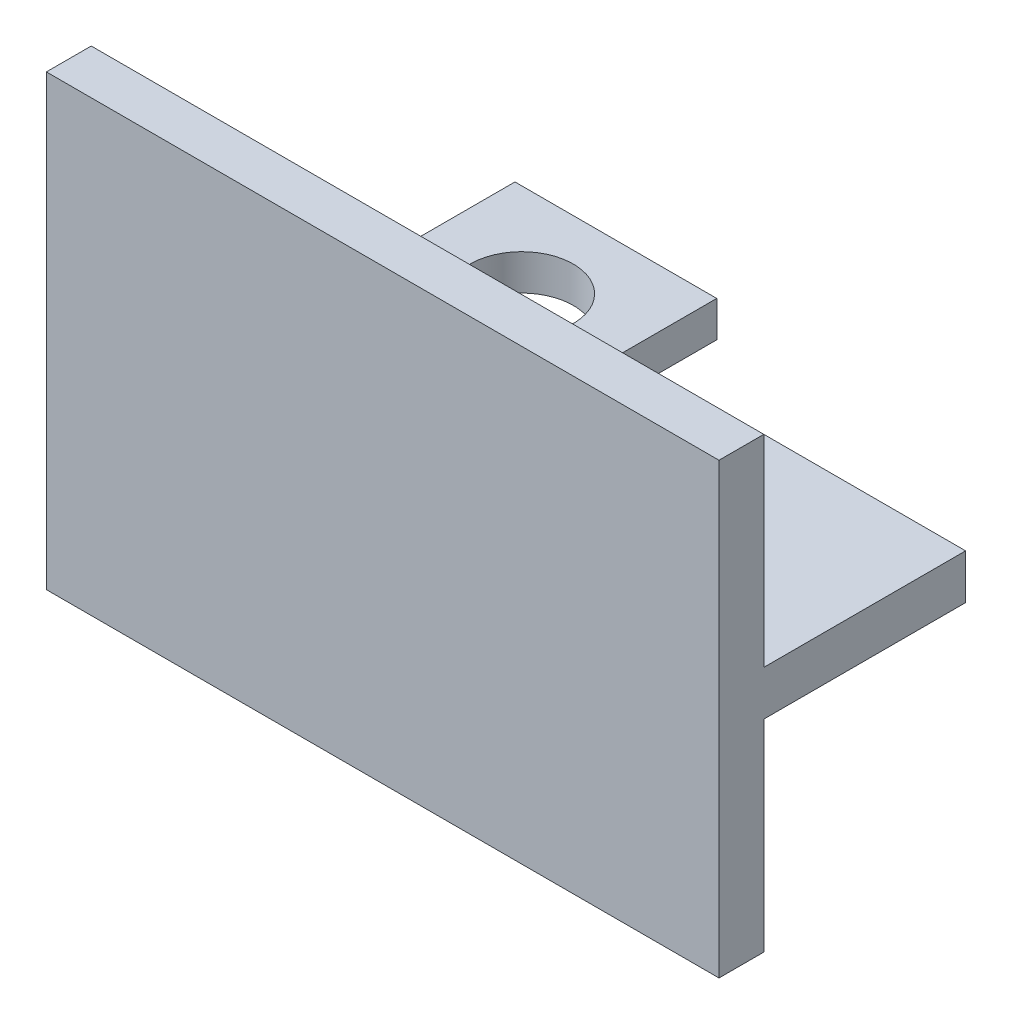
SolidWorks part; units mm, degrees
ref_plane "Plan de face" through (0, 0, 0) normal (0, 0, 1) x (1, 0, 0)
ref_plane "Plan de dessus" through (0, 0, 0) normal (0, 1, 0) x (1, 0, 0)
ref_plane "Plan de droite" through (0, 0, 0) normal (1, 0, 0) x (0, 0, -1)
sketch "Sketch1" plane through (0, 0, 0) normal (0, 0, 1) x (1, 0, 0)
  line L0 (187.7509, 883.2503) -> (187.7509, 873.2503)
  line L1 (37.7509, 883.2503) -> (187.7509, 883.2503)
  line L2 (37.7509, 883.2503) -> (37.7509, 873.2503)
  line L5 (187.7509, 873.2503) -> (37.7509, 873.2503)
  dimension "D1" = 10
  dimension "D2" = 150
extrude "Boss-Extrude1" add sketch "Sketch1" against normal blind 55
sketch "Sketch2" plane through (0, 883.2503, 0) normal (0, 1, 0) x (1, 0, 0)
  line L0 (187.7509, 55) -> (187.7509, 0) construction
  line L1 (37.7509, 0) -> (187.7509, 0)
  line L2 (37.7509, 0) -> (37.7509, 10)
  line L3 (37.7509, 10) -> (187.7509, 10)
  line L4 (187.7509, 0) -> (187.7509, 10)
  dimension "D1" = 10
extrude "Boss-Extrude2" add sketch "Sketch2" along normal blind 45 and the other way blind 55 contours L3 L4 L1 L2
sketch "Sketch3" plane through (0, 0, -10) normal (0, 0, -1) x (-1, 0, 0)
  line L0 (-112.7509, 928.2503) -> (-112.7509, 903.2503) construction
  line L1 (-135.2509, 899.2503) -> (-90.2509, 899.2503)
  line L2 (-135.2509, 899.2503) -> (-135.2509, 907.2503)
  line L3 (-135.2509, 907.2503) -> (-90.2509, 907.2503)
  line L4 (-90.2509, 899.2503) -> (-90.2509, 907.2503)
  line L5 (-135.2509, 899.2503) -> (-90.2509, 907.2503) construction
  line L6 (-135.2509, 907.2503) -> (-90.2509, 899.2503) construction
  line L7 (-37.7509, 928.2503) -> (-187.7509, 928.2503) construction
  point P0 (-112.7509, 903.2503)
  dimension "D1" = 45
  dimension "D2" = 8
  dimension "D3" = 25
extrude "Boss-Extrude3" add sketch "Sketch3" along normal blind 42 contours L3 L4 L1 L2
sketch "Sketch4" plane through (0, 883.2503, 0) normal (0, 1, 0) x (1, 0, 0)
  line L0 (187.7509, 55) -> (37.7509, 55) construction
  line L1 (84.8162, 10) -> (141.3368, 10)
  line L2 (84.8162, 10) -> (84.8162, 55)
  line L3 (84.8162, 55) -> (141.3368, 55)
  line L4 (141.3368, 10) -> (141.3368, 55)
  line L5 (84.8162, 10) -> (141.3368, 55) construction
  line L6 (84.8162, 55) -> (141.3368, 10) construction
  line L7 (37.7509, 10) -> (187.7509, 10) construction
  point P0 (113.0765, 32.5)
extrude "Cut-Extrude1" cut sketch "Sketch4" against normal through all contours L4 L3 L2 L1
sketch "Sketch5" plane through (0, 907.2503, 0) normal (0, 1, 0) x (1, 0, 0)
  line L0 (112.7509, 52) -> (112.7509, 10) construction
  line L1 (135.2509, 52) -> (90.2509, 52) construction
  line L2 (135.2509, 10) -> (90.2509, 10) construction
  line L3 (112.7509, 10) -> (90.2509, 31) construction
  line L4 (90.2509, 52) -> (90.2509, 10) construction
  line L5 (90.2509, 31) -> (112.6009, 31.15) construction
  circle A0 centre (112.6009, 31.15) radius 11.5
  dimension "D1" = 23
extrude "Cut-Extrude2" cut sketch "Sketch5" against normal through all
